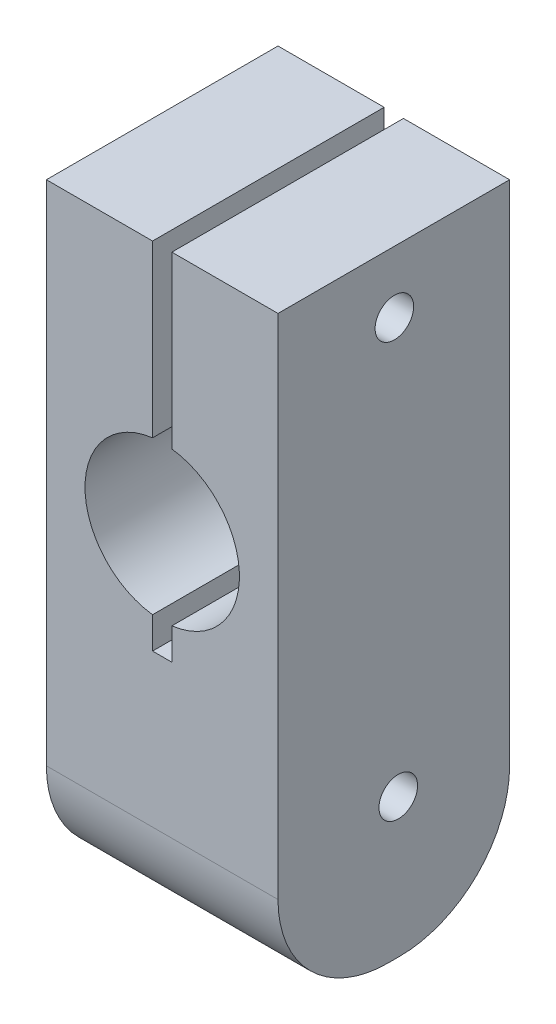
SolidWorks part; units mm, degrees
ref_plane "Front" through (0, 0, 0) normal (0, 0, 1) x (1, 0, 0)
ref_plane "Top" through (0, 0, 0) normal (0, 1, 0) x (1, 0, 0)
ref_plane "Right" through (0, 0, 0) normal (1, 0, 0) x (0, 0, -1)
sketch "Sketch1" plane through (0, 0, 0) normal (0, 1, 0) x (1, 0, 0)
  line L1 (-9.525, 9.525) -> (9.525, 9.525)
  line L2 (-9.525, 9.525) -> (-9.525, -9.525)
  line L3 (-9.525, -9.525) -> (9.525, -9.525)
  line L4 (9.525, 9.525) -> (9.525, -9.525)
  line L5 (-9.525, 9.525) -> (9.525, -9.525) construction
  line L6 (-9.525, -9.525) -> (9.525, 9.525) construction
  point P0 (0, 0)
extrude "Boss-Extrude1" add sketch "Sketch1" along normal blind 50.8
sketch "Sketch4" plane through (0, 50.8, 0) normal (0, 1, 0) x (1, 0, 0)
  line L0 (0, 9.525) -> (0, -9.525) construction
  line L1 (9.525, 9.525) -> (-9.525, 9.525) construction
  line L2 (-9.525, -9.525) -> (9.525, -9.525) construction
  line L4 (-0.7937, 9.525) -> (0.7937, 9.525)
  line L5 (-0.7937, 9.525) -> (-0.7937, -9.525)
  line L6 (-0.7937, -9.525) -> (0.7937, -9.525)
  line L7 (0.7937, 9.525) -> (0.7937, -9.525)
  line L8 (-0.7937, 9.525) -> (0.7937, -9.525) construction
  line L9 (-0.7937, -9.525) -> (0.7937, 9.525) construction
  point P6 (0, 0)
extrude "Cut-Extrude1" cut sketch "Sketch4" against normal blind 29.21
sketch "Sketch5" plane through (0, 0, 9.525) normal (0, 0, 1) x (1, 0, 0)
  circle A2 centre (0, 30.48) radius 6.35
extrude "Cut-Extrude2" cut sketch "Sketch5" against normal up to next
fillet "Fillet3" radius 9.05 2 edges at (0, 0, -9.525) (0, 0, 9.525)
sketch "Sketch6" plane through (9.525, 0, 0) normal (1, 0, 0) x (0, 0, -1)
  circle A0 centre (0.0475, 45.7202) radius 1.5875
  circle A1 centre (0.3681, 11.4317) radius 1.5875
extrude "Cut-Extrude3" cut sketch "Sketch6" against normal up to surface (19.05 mm away) up to face at (-9.525, 19.3252, 0)
